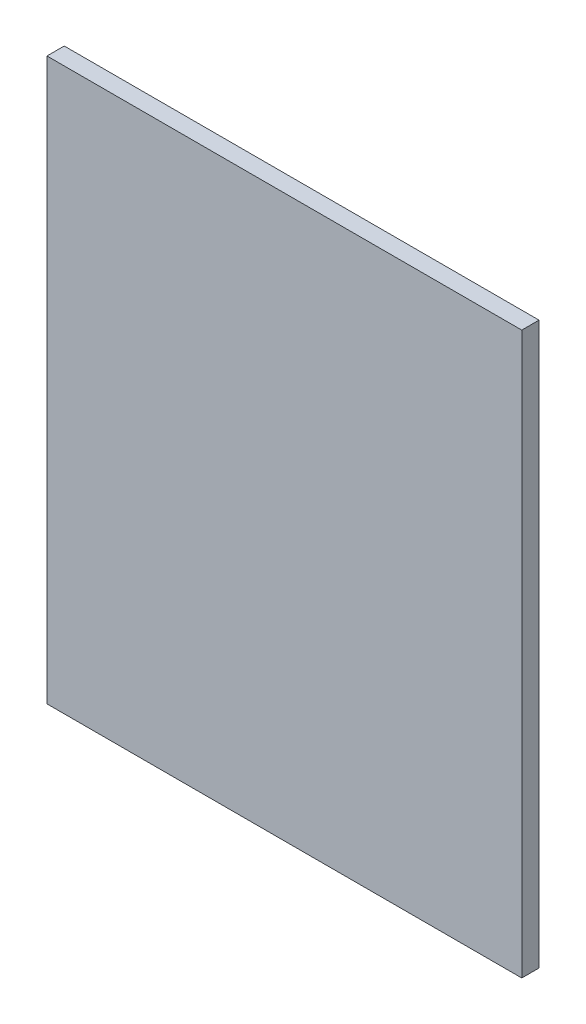
SolidWorks part; units mm, degrees
ref_plane "前视基准面" through (0, 0, 0) normal (0, 0, 1) x (1, 0, 0)
ref_plane "上视基准面" through (0, 0, 0) normal (0, 1, 0) x (1, 0, 0)
ref_plane "右视基准面" through (0, 0, 0) normal (1, 0, 0) x (0, 0, -1)
sketch "草图1" plane through (0, 0, 0) normal (0, 0, 1) x (1, 0, 0)
  line L1 (-275, -325) -> (275, -325)
  line L2 (-275, -325) -> (-275, 325)
  line L3 (-275, 325) -> (275, 325)
  line L4 (275, -325) -> (275, 325)
  line L5 (-275, -325) -> (275, 325) construction
  line L6 (-275, 325) -> (275, -325) construction
  point P0 (0, 0)
  dimension "D1" = 650
  dimension "D2" = 550
extrude "凸台-拉伸1" add sketch "草图1" along normal blind 20
